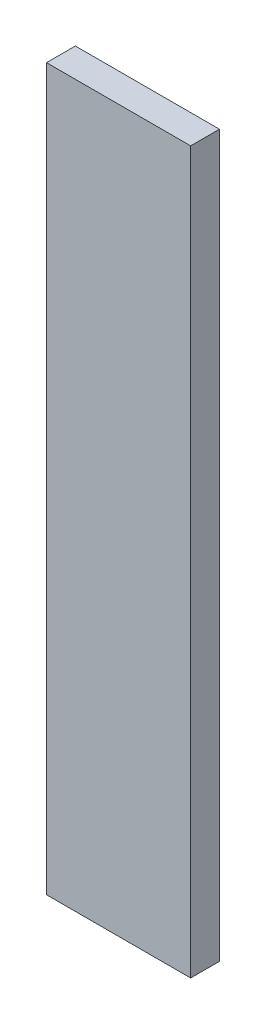
SolidWorks part; units mm, degrees
ref_plane "Спереди" through (0, 0, 0) normal (0, 0, 1) x (1, 0, 0)
ref_plane "Сверху" through (0, 0, 0) normal (0, 1, 0) x (1, 0, 0)
ref_plane "Справа" through (0, 0, 0) normal (1, 0, 0) x (0, 0, -1)
sketch "Эскиз1" plane through (0, 0, 0) normal (0, 1, 0) x (1, 0, 0)
  line L1 (0, 0) -> (10, 0)
  line L2 (0, 0) -> (0, 2)
  line L3 (0, 2) -> (10, 2)
  line L4 (10, 0) -> (10, 2)
extrude "Бобышка-Вытянуть1" add sketch "Эскиз1" along normal blind 50
